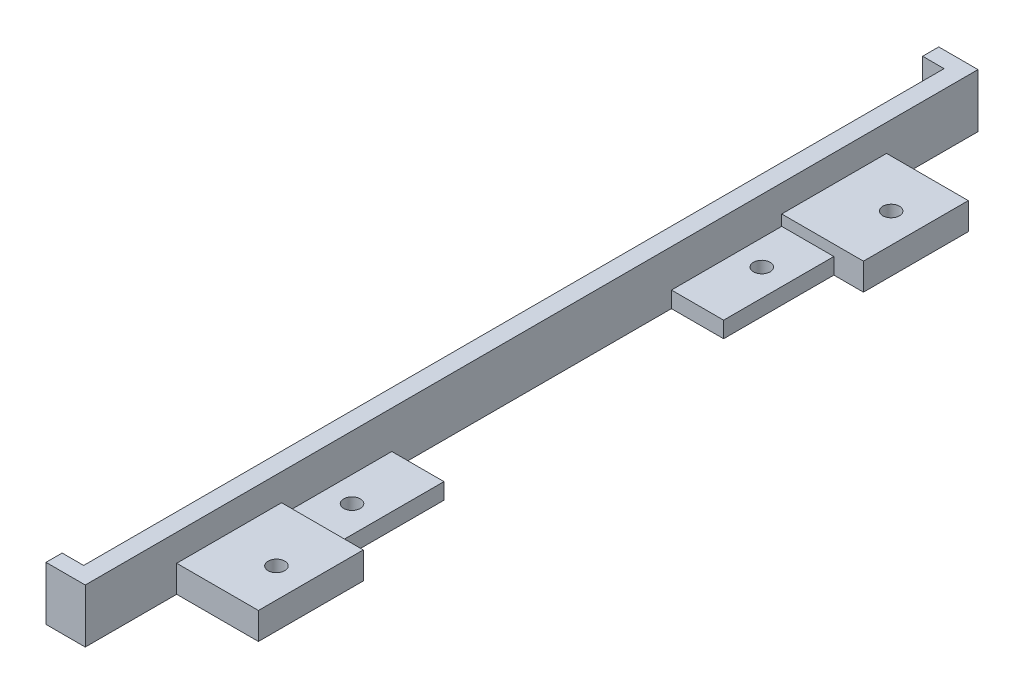
SolidWorks part; units mm, degrees
ref_plane "Front Plane" through (0, 0, 0) normal (0, 0, 1) x (1, 0, 0)
ref_plane "Top Plane" through (0, 0, 0) normal (0, 1, 0) x (1, 0, 0)
ref_plane "Right Plane" through (0, 0, 0) normal (1, 0, 0) x (0, 0, -1)
sketch "Sketch1" plane through (0, 0, 0) normal (0, 1, 0) x (1, 0, 0)
  line L0 (0, 0) -> (7.3, 0)
  line L1 (7.3, 0) -> (7.3, 17)
  line L2 (7.3, 17) -> (22.5, 17)
  line L3 (22.5, 17) -> (22.5, 36.5)
  line L4 (22.5, 36.5) -> (17, 36.5)
  line L5 (17, 36.5) -> (17, 57)
  line L6 (17, 57) -> (7.3, 57)
  line L7 (7.3, 57) -> (7.3, 109)
  line L8 (0, 0) -> (0, 3)
  line L9 (0, 3) -> (4, 3)
  line L10 (4, 3) -> (4, 163)
  line L11 (7.3, 83) -> (4, 83) construction
  line L12 (17, 109) -> (7.3, 109)
  line L13 (17, 129.5) -> (17, 109)
  line L14 (22.5, 129.5) -> (17, 129.5)
  line L15 (22.5, 149) -> (22.5, 129.5)
  line L16 (7.3, 149) -> (22.5, 149)
  line L17 (7.3, 166) -> (7.3, 149)
  line L18 (0, 163) -> (4, 163)
  line L19 (0, 166) -> (7.3, 166)
  line L20 (0, 166) -> (0, 163)
  circle A0 centre (17, 25.85) radius 1.55
  circle A1 centre (12, 44.9) radius 1.55
  circle A2 centre (12, 121.1) radius 1.55
  circle A3 centre (17, 140.15) radius 1.55
  dimension "D10" = 3.1
  dimension "D11" = 3.1
  dimension "D12" = 76.2
  dimension "D13" = 114.3
  dimension "D2" = 3
  dimension "D3" = 17
  dimension "D4" = 19.5
  dimension "D5" = 40
  dimension "D6" = 160
  dimension "D7" = 3.3
  dimension "D8" = 18.5
  dimension "D9" = 13
  dimension "D14" = 8
  dimension "D15" = 7.3
extrude "Boss-Extrude1" add sketch "Sketch1" along normal blind 10
sketch "Sketch3" plane through (0, 10, 0) normal (0, 1, 0) x (1, 0, 0)
  line L0 (7.3, 149) -> (22.5, 149)
  line L1 (22.5, 149) -> (22.5, 17)
  line L2 (22.5, 17) -> (7.3, 17)
  line L3 (7.3, 17) -> (7.3, 149)
extrude "Cut-Extrude1" cut sketch "Sketch3" against normal blind 5
sketch "Sketch4" plane through (0, 5, 0) normal (0, 1, 0) x (1, 0, 0)
  line L0 (17, 129.5) -> (17, 36.5)
  line L1 (17, 36.5) -> (7.3, 36.5)
  line L2 (7.3, 57) -> (7.3, 17) construction
  line L3 (7.3, 36.5) -> (7.3, 129.5)
  line L4 (7.3, 149) -> (7.3, 109) construction
  line L5 (7.3, 129.5) -> (17, 129.5)
extrude "Cut-Extrude2" cut sketch "Sketch4" against normal blind 2
sketch "Sketch5" plane through (0, 0, 0) normal (0, -1, 0) x (1, 0, 0)
  line L0 (17, -25.85) -> (19.75, -25.85) construction
  line L1 (19.75, -24.2623) -> (19.75, -27.4377)
  line L2 (17, -25.85) -> (18.375, -28.2316) construction
  line L3 (19.75, -27.4377) -> (17, -29.0254)
  line L4 (17, -25.85) -> (15.625, -28.2316) construction
  line L5 (17, -29.0254) -> (14.25, -27.4377)
  line L6 (17, -25.85) -> (14.25, -25.85) construction
  line L7 (14.25, -27.4377) -> (14.25, -24.2623)
  line L8 (17, -25.85) -> (15.625, -23.4684) construction
  line L9 (14.25, -24.2623) -> (17, -22.6746)
  line L10 (17, -25.85) -> (18.375, -23.4684) construction
  line L11 (17, -22.6746) -> (19.75, -24.2623)
  line L12 (4, -83) -> (14.7, -83) construction
  line L13 (4, -163) -> (4, -3) construction
  line L14 (14.25, -138.5623) -> (14.25, -141.7377)
  line L15 (17, -136.9746) -> (14.25, -138.5623)
  line L16 (19.75, -138.5623) -> (17, -136.9746)
  line L17 (19.75, -141.7377) -> (19.75, -138.5623)
  line L18 (17, -143.3254) -> (19.75, -141.7377)
  line L19 (14.25, -141.7377) -> (17, -143.3254)
  point P7 (19.75, -25.85)
  point P25 (17, -25.85)
  dimension "D1" = 6
  dimension "D2" = 5.5
extrude "Cut-Extrude4" cut sketch "Sketch5" against normal blind 2.3
